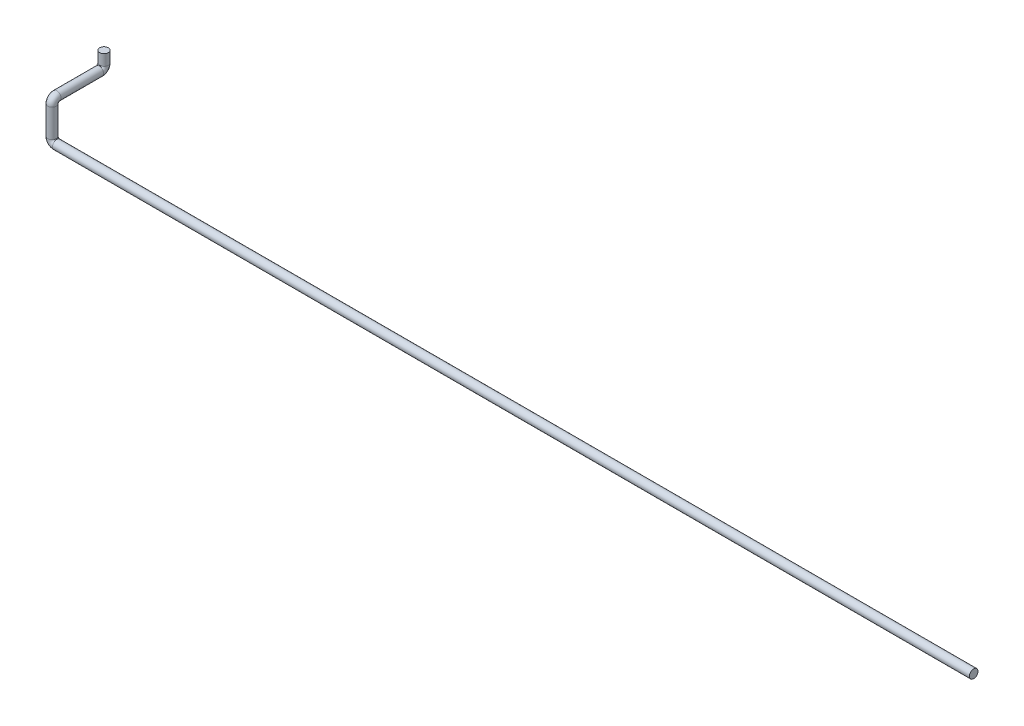
SolidWorks part; units mm, degrees
ref_plane "Alzado" through (0, 0, 0) normal (0, 0, 1) x (1, 0, 0)
ref_plane "Planta" through (0, 0, 0) normal (0, 1, 0) x (1, 0, 0)
ref_plane "Vista lateral" through (0, 0, 0) normal (1, 0, 0) x (0, 0, -1)
sketch3d "Croquis3D1"
  line L0 (0, 0, 0) -> (-2930, 0, 0)
  line L1 (-2945, 15, 0) -> (-2945, 105, 0)
  line L2 (-2945, 120, -15) -> (-2945, 120, -151)
  line L3 (-2945, 135, -166) -> (-2945, 170, -166)
  arc A0 (-2945, 120, -151) -> (-2945, 135, -166) centre (-2945, 135, -151) ccw
  arc A1 (-2945, 105, 0) -> (-2945, 120, -15) centre (-2945, 105, -15) ccw
  arc A2 (-2930, 0, 0) -> (-2945, 15, 0) centre (-2930, 15, 0) ccw
  point P8 (-2945, 120, -166)
  point P9 (-2930, 135, -151)
  point P12 (-2945, 120, 0)
  point P13 (-2960, 105, -15)
  point P16 (-2945, 0, 0)
  point P17 (-2930, 15, -15)
  dimension "D5" = 15
  dimension "D1" = 2945
  dimension "D2" = 120
  dimension "D3" = 166
  dimension "D4" = 50
sketch "Croquis1" plane through (0, 0, 0) normal (1, 0, 0) x (0, 0, -1)
  circle A0 centre (0, 0) radius 13.7
  dimension "D1" = 27.4
sweep "Barrer1" add profiles "Croquis1" path "Croquis3D1"
